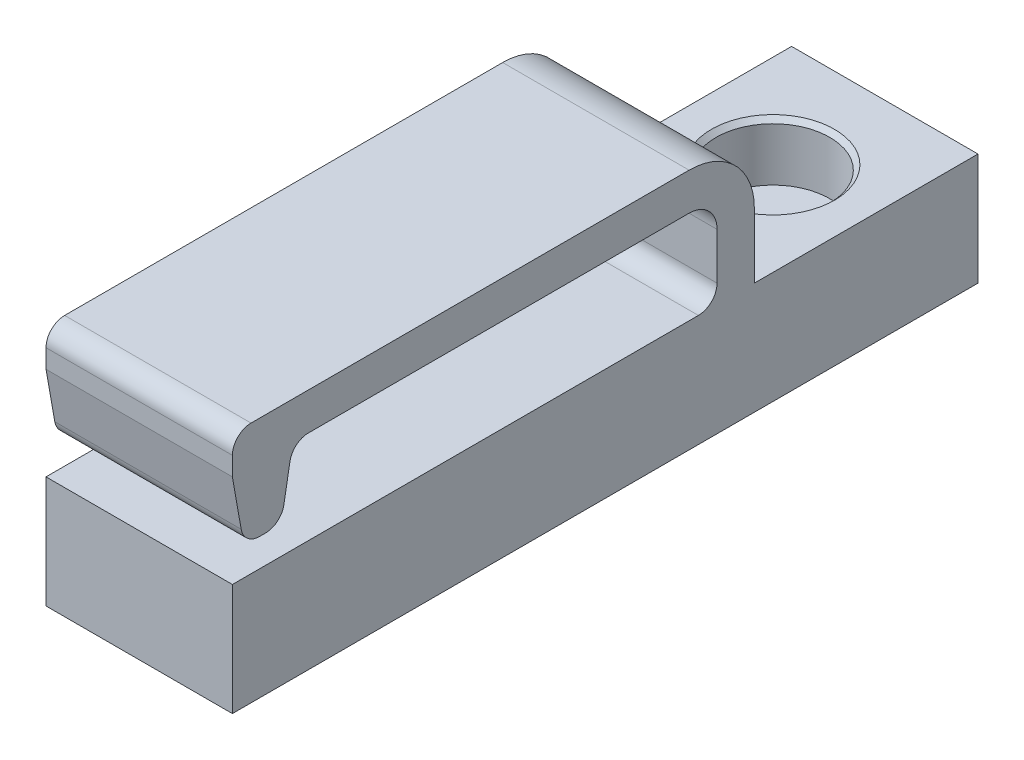
SolidWorks part; units mm, degrees
ref_plane "Front Plane" through (0, 0, 0) normal (0, 0, 1) x (1, 0, 0)
ref_plane "Top Plane" through (0, 0, 0) normal (0, 1, 0) x (1, 0, 0)
ref_plane "Right Plane" through (0, 0, 0) normal (1, 0, 0) x (0, 0, -1)
sketch "Sketch1" plane through (0, 0, 0) normal (0, 1, 0) x (1, 0, 0)
  line L1 (0, 0) -> (10, 0)
  line L2 (0, 0) -> (0, -40)
  line L3 (0, -40) -> (10, -40)
  line L4 (10, 0) -> (10, -40)
  dimension "D1" = 10
  dimension "D2" = 40
extrude "Boss-Extrude1" add sketch "Sketch1" along normal blind 6
sketch "Sketch2" plane through (0, 6, 0) normal (0, 1, 0) x (1, 0, 0)
  line L0 (5, 0) -> (5, -12) construction
  line L1 (10, 0) -> (0, 0) construction
  circle A0 centre (5, -6) radius 3.05
  point P4 (5, -6)
  dimension "D2" = 6.1
  dimension "D1" = 12
ref_plane "Plane1" through (5, 0, 0) normal (-1, 0, 0) x (0, 0, 1)
extrude "Cut-Extrude1" cut sketch "Sketch2" against normal blind 3.1
chamfer "Chamfer1" distance 0.25 angle 45 1 edges at (5, 6, 9.05)
sketch "Sketch4" plane through (5, 0, 0) normal (-1, 0, 0) x (0, 0, 1)
  line L0 (0, 6) -> (12, 6) construction
  line L1 (0, 6) -> (40, 6) construction
  line L2 (12, 6) -> (12, 13)
  line L3 (12, 13) -> (40, 13)
  line L4 (40, 13) -> (40, 11)
  line L5 (40, 11) -> (39.3829, 7.5)
  line L6 (39.3829, 7.5) -> (37.3829, 7.5)
  line L7 (37.3829, 7.5) -> (36.7657, 11)
  line L8 (36.7657, 11) -> (14, 11)
  line L9 (14, 11) -> (14, 6)
  line L10 (14, 6) -> (12, 6)
  line L11 (40, 6) -> (40, 0) construction
  line L12 (25.3829, 11) -> (25.3829, 6) construction
  circle A0 centre (25.3829, 8.5) radius 2.5 construction
  dimension "D4" = 5
  dimension "D1" = 12
  dimension "D2" = 2
  dimension "D3" = 2
  dimension "D5" = 1.5
  dimension "D6" = 100
  dimension "D7" = 100
  dimension "D8" = 2
extrude "Boss-Extrude2" add sketch "Sketch4" along normal mid plane 10
fillet "Fillet1" radius 1.5 1 edges at (5, 11, 14)
fillet "Fillet2" radius 3.5 1 edges at (5, 13, 12)
fillet "Fillet3" radius 1 1 edges at (5, 6, 14)
fillet "Fillet4" radius 1 4 edges at (5, 11, 36.7657) (5, 7.5, 37.3829) (5, 7.5, 39.3829) (5, 13, 40)
equation "\"D3@Sketch4\"=\"D2@Sketch4\""
equation "\"D7@Sketch4\"=\"D6@Sketch4\""
